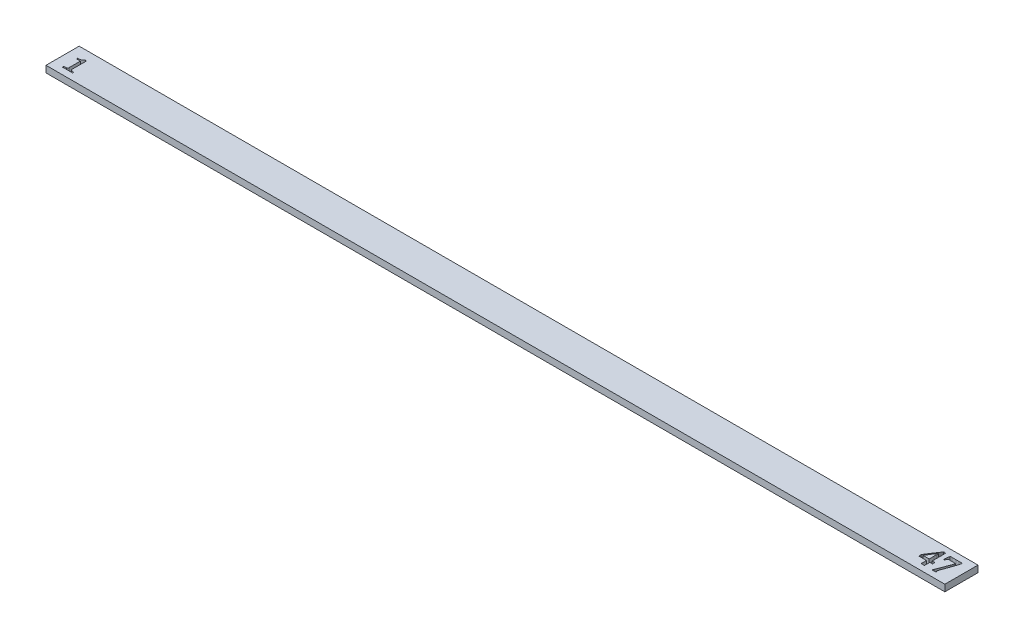
SolidWorks part; units mm, degrees
ref_plane "Front Plane" through (0, 0, 0) normal (0, 0, 1) x (1, 0, 0)
ref_plane "Top Plane" through (0, 0, 0) normal (0, 1, 0) x (1, 0, 0)
ref_plane "Right Plane" through (0, 0, 0) normal (1, 0, 0) x (0, 0, -1)
sketch "Sketch1" plane through (0, 0, 0) normal (0, 1, 0) x (1, 0, 0)
  line L1 (0, 0) -> (406.5, 0)
  line L2 (0, 0) -> (0, 15)
  line L3 (0, 15) -> (406.5, 15)
  line L4 (406.5, 0) -> (406.5, 15)
  dimension "D1" = 406.5
  dimension "D2" = 15
extrude "Boss-Extrude1" add sketch "Sketch1" along normal blind 3 contours L2 L1 L4 L3
sketch "Sketch6" plane through (0, 3, 0) normal (0, 1, 0) x (1, 0, 0)
  line L0 (9.0667, 3) -> (4.4, 3)
  line L1 (4.4, 3) -> (4.4, 3.5333)
  line L2 (6.1333, 4.4021) -> (6.1333, 9.4)
  line L3 (6.1333, 9.4) -> (4.4, 9.4)
  line L4 (4.4, 9.4) -> (4.4, 9.9333)
  line L5 (4.4, 9.9333) -> (4.7708, 9.9333)
  line L6 (6.9063, 10.8667) -> (7.4667, 10.8667)
  line L7 (7.4667, 8.6813) -> (7.4667, 4.4771)
  line L8 (9.0667, 3.5333) -> (9.0667, 3)
  spline S0 degree 3 poles (4.4, 3.5333) (4.4906, 3.5373) (4.6409, 3.5544) (4.8612, 3.5732) (5.0605, 3.5939) (5.2574, 3.6135) (5.4646, 3.6453) (5.603, 3.6659) (5.6813, 3.6896) knots 0 0 0 0 0.21039 0.351267 0.513318 0.675537 0.810763 1 1 1 1
  spline S1 degree 3 poles (5.6813, 3.6896) (5.7489, 3.7133) (5.8461, 3.7566) (5.9542, 3.8436) (6.0199, 3.9204) (6.0747, 4.0123) (6.1218, 4.1744) (6.1362, 4.3073) (6.1333, 4.4021) knots 0 0 0 0 0.235251 0.343488 0.451439 0.564461 0.690935 1 1 1 1
  spline S2 degree 3 poles (4.7708, 9.9333) (5.0033, 9.9326) (5.3457, 9.9689) (5.7802, 10.0922) (6.0742, 10.2224) (6.34, 10.3701) (6.6302, 10.5692) (6.8142, 10.7396) (6.9063, 10.8667) knots 0 0 0 0 0.289649 0.426683 0.561658 0.689593 0.805376 1 1 1 1
  spline S3 degree 3 poles (7.4667, 10.8667) (7.4667, 10.7) (7.4667, 10.4403) (7.4667, 10.0806) (7.4667, 9.5187) (7.4667, 9.05) (7.4667, 8.6813) knots 0 0 0 0 0.228789 0.35653 0.493804 1 1 1 1
  spline S4 degree 3 poles (7.4667, 4.4771) (7.4652, 4.3238) (7.5089, 4.1322) (7.6276, 3.9406) (7.7255, 3.8361) (7.8135, 3.7747) (7.8792, 3.7458) knots 0 0 0 0 0.518336 0.640812 0.758815 1 1 1 1
  spline S5 degree 3 poles (7.8792, 3.7458) (7.9543, 3.7133) (8.0861, 3.6778) (8.2812, 3.6344) (8.4608, 3.6037) (8.6413, 3.5752) (8.8434, 3.5503) (8.9822, 3.5352) (9.0667, 3.5333) knots 0 0 0 0 0.202205 0.337958 0.495327 0.653832 0.79092 1 1 1 1
extrude "Cut-Extrude3" cut sketch "Sketch6" against normal blind 3
sketch "Sketch7" plane through (0, 3, 0) normal (0, 1, 0) x (1, 0, 0)
  line L0 (0, 3) -> (406.5, 3)
  line L1 (0, 0) -> (0, 15) construction
  line L2 (406.5, 0) -> (406.5, 15) construction
  line L3 (0, 0) -> (406.5, 0) construction
  line L4 (397.6574, 12.1343) -> (399.3617, 12.1196)
  line L5 (399.3617, 12.1196) -> (400.8036, 12.1343)
  line L6 (400.8036, 12.1343) -> (401.6306, 12.1343)
  line L7 (401.6306, 12.1343) -> (401.916, 12.1343)
  line L8 (400.791, 7.2481) -> (400.4405, 6.2512)
  line L9 (400.1047, 5.3193) -> (399.5317, 3.7031)
  line L10 (399.5968, 2.7313) -> (399.4142, 2.7313)
  line L11 (399.4142, 2.7313) -> (398.8874, 2.7397)
  line L12 (399.007, 5.3046) -> (400.2642, 8.6943)
  line L13 (400.2642, 8.6943) -> (400.5791, 9.559)
  line L14 (399.7899, 10.5224) -> (398.7341, 10.5056)
  line L15 (398.7341, 10.5056) -> (397.8904, 10.5224)
  line L16 (395.7537, 6.2239) -> (395.7537, 5.1493)
  line L17 (394.5448, 4.9415) -> (394.5448, 4.5133)
  line L18 (394.5448, 4.5133) -> (394.5448, 4.0557)
  line L19 (394.5448, 4.0557) -> (394.5448, 3.7409)
  line L20 (394.5448, 2.7313) -> (393.9403, 2.7313)
  line L21 (393.9403, 2.7313) -> (393.5667, 2.7313)
  line L22 (393.3421, 2.7313) -> (393.2225, 2.7313)
  line L23 (393.0672, 2.7313) -> (393.0672, 4.1187)
  line L24 (393.0672, 4.1187) -> (393.0672, 5.0128)
  line L25 (392.0408, 5.1493) -> (391.5686, 5.1493)
  line L26 (389.5746, 5.1493) -> (389.5746, 5.2206)
  line L27 (389.5746, 5.2206) -> (389.5746, 5.6719)
  line L28 (389.5746, 5.6719) -> (389.5746, 5.8167)
  line L29 (389.5746, 5.8167) -> (389.5746, 6.0854)
  line L30 (389.5746, 6.0854) -> (389.5746, 6.1378)
  line L31 (389.9944, 6.9984) -> (391.6504, 9.559)
  line L32 (394.5448, 12.382) -> (394.5448, 12.2938)
  line L33 (394.5448, 12.2938) -> (394.5448, 11.746)
  line L34 (394.5448, 11.746) -> (394.5448, 11.555)
  line L35 (394.5448, 11.555) -> (394.5448, 11.2507)
  line L36 (394.5448, 11.2507) -> (394.5448, 10.9485)
  line L37 (394.5448, 10.9485) -> (394.5448, 10.216)
  line L38 (394.5448, 10.216) -> (394.5448, 9.899)
  line L39 (394.5448, 9.899) -> (394.5448, 9.4834)
  line L40 (394.5448, 9.4834) -> (394.5448, 9.0993)
  line L41 (394.5448, 9.0993) -> (394.5448, 8.5746)
  line L42 (394.5448, 8.5746) -> (394.5448, 8.073)
  line L43 (394.5448, 8.073) -> (394.5448, 7.4874)
  line L44 (394.5448, 7.4874) -> (394.5448, 6.2239)
  line L45 (395.2059, 6.2239) -> (395.3885, 6.2239)
  line L46 (393.0672, 7.4307) -> (393.0672, 7.9953)
  line L47 (393.0672, 7.9953) -> (393.0672, 8.4802)
  line L48 (393.0672, 8.4802) -> (393.0735, 9.7332)
  line L49 (393.0735, 9.7332) -> (393.0672, 10.3062)
  line L50 (392.0933, 9.2778) -> (391.4489, 8.2346)
  line L51 (390.6283, 6.3582) -> (390.9788, 6.3582)
  line L52 (390.9788, 6.3582) -> (391.6777, 6.3582)
  line L53 (391.6777, 6.3582) -> (392.6516, 6.3582)
  line L54 (392.6516, 6.3582) -> (393.0672, 6.3582)
  spline S0 degree 3 poles (396.7885, 12.1343) (396.9074, 12.1343) (397.1971, 12.1343) (397.4867, 12.1343) (397.6574, 12.1343) knots 0 0 0 0 0.410628 1 1 1 1
  spline S1 degree 2 poles (401.916, 12.1343) (402.0483, 12.1343) (402.1805, 12.1343) knots 0 0 0 1 1 1
  spline S2 degree 2 poles (402.1805, 12.1343) (402.2016, 11.9249) (402.2015, 11.7146) knots 0 0 0 1 1 1
  spline S3 degree 3 poles (402.2015, 11.7146) (402.2031, 11.6686) (402.1907, 11.5918) (402.1741, 11.4778) (402.1522, 11.3659) (402.1251, 11.2364) (402.0773, 11.0283) (402.0357, 10.8643) (402.0063, 10.7491) knots 0 0 0 0 0.13905 0.235946 0.350701 0.485483 0.638259 1 1 1 1
  spline S4 degree 3 poles (402.0063, 10.7491) (401.8713, 10.3858) (401.7226, 9.9355) (401.555, 9.4149) (401.4732, 9.1593) (401.4146, 8.9873) (401.3766, 8.8853) knots 0 0 0 0 0.590758 0.723007 0.834001 1 1 1 1
  spline S5 degree 3 poles (401.3766, 8.8853) (401.3139, 8.7235) (401.2049, 8.4219) (401.1038, 8.1175) (401.0618, 7.9764) knots 0 0 0 0 0.54115 1 1 1 1
  spline S6 degree 3 poles (401.0618, 7.9764) (401.0158, 7.8672) (400.9261, 7.6242) (400.8365, 7.3811) (400.791, 7.2481) knots 0 0 0 0 0.457479 1 1 1 1
  spline S7 degree 3 poles (400.4405, 6.2512) (400.4019, 6.129) (400.2893, 5.8185) (400.1773, 5.5079) (400.1047, 5.3193) knots 0 0 0 0 0.387978 1 1 1 1
  spline S8 degree 2 poles (399.5317, 3.7031) (399.4708, 3.5883) (399.4583, 3.4597) knots 0 0 0 1 1 1
  spline S9 degree 3 poles (399.4583, 3.4597) (399.4594, 3.4188) (399.4839, 3.3553) (399.5515, 3.2864) (399.6193, 3.235) (399.6889, 3.1853) (399.757, 3.1186) (399.7825, 3.0565) (399.7836, 3.0168) knots 0 0 0 0 0.21312 0.343422 0.503307 0.660927 0.793754 1 1 1 1
  spline S10 degree 3 poles (399.7836, 3.0168) (399.7823, 2.9669) (399.7381, 2.8546) (399.6492, 2.7737) (399.5968, 2.7313) knots 0 0 0 0 0.419347 1 1 1 1
  spline S11 degree 3 poles (398.8874, 2.7397) (398.8602, 2.7429) (398.809, 2.7411) (398.7271, 2.7429) (398.565, 2.7317) (398.4263, 2.7344) (398.3186, 2.7313) knots 0 0 0 0 0.143976 0.269387 0.431851 1 1 1 1
  spline S12 degree 2 poles (398.3186, 2.7313) (398.1779, 2.7313) (398.0373, 2.7313) knots 0 0 0 1 1 1
  spline S13 degree 3 poles (398.0373, 2.7313) (398.0497, 2.8378) (398.136, 3.1077) (398.2523, 3.3648) (398.3249, 3.5247) knots 0 0 0 0 0.377761 1 1 1 1
  spline S14 degree 3 poles (398.3249, 3.5247) (398.3592, 3.6042) (398.417, 3.7399) (398.4975, 3.9457) (398.5768, 4.1509) (398.6699, 4.3903) (398.8144, 4.7787) (398.9266, 5.0879) (399.007, 5.3046) knots 0 0 0 0 0.13619 0.232079 0.347806 0.482346 0.636339 1 1 1 1
  spline S15 degree 3 poles (400.5791, 9.559) (400.6161, 9.6353) (400.6856, 9.8169) (400.7493, 10.0004) (400.7826, 10.1047) knots 0 0 0 0 0.436195 1 1 1 1
  spline S16 degree 3 poles (400.7826, 10.1047) (400.7964, 10.1557) (400.8489, 10.2789) (400.8843, 10.4082) (400.917, 10.4825) knots 0 0 0 0 0.394055 1 1 1 1
  spline S17 degree 3 poles (400.917, 10.4825) (400.7072, 10.4941) (400.3316, 10.5116) (399.9558, 10.5235) (399.7899, 10.5224) knots 0 0 0 0 0.558859 1 1 1 1
  spline S18 degree 3 poles (397.8904, 10.5224) (397.7795, 10.5191) (397.6233, 10.5162) (397.4439, 10.4576) (397.3479, 10.402) (397.2801, 10.3185) (397.2259, 10.2157) (397.1823, 10.0881) (397.1537, 9.9447) (397.1276, 9.8052) (397.098, 9.6861) (397.0621, 9.5983) (397.0277, 9.5316) (396.9769, 9.4939) (396.8959, 9.4512) (396.8197, 9.4525) (396.7696, 9.4478) knots 0 0 0 0 0.189213 0.259177 0.317619 0.373826 0.438412 0.513621 0.600884 0.685342 0.753932 0.807539 0.846294 0.87826 0.912652 1 1 1 1
  spline S19 degree 3 poles (396.7696, 9.4478) (396.7096, 9.4441) (396.5726, 9.511) (396.5612, 9.6645) (396.5597, 9.7332) knots 0 0 0 0 0.447089 1 1 1 1
  spline S20 degree 3 poles (396.5597, 9.7332) (396.5577, 9.8826) (396.5859, 10.2424) (396.6123, 10.6021) (396.6395, 10.812) knots 0 0 0 0 0.413664 1 1 1 1
  spline S21 degree 3 poles (396.6395, 10.812) (396.6743, 11.0497) (396.712, 11.4917) (396.7566, 11.9331) (396.7885, 12.1343) knots 0 0 0 0 0.541005 1 1 1 1
  spline S22 degree 3 poles (395.7537, 5.1493) (395.6313, 5.1493) (395.4158, 5.1493) (395.2003, 5.1493) (395.1073, 5.1493) knots 0 0 0 0 0.568182 1 1 1 1
  spline S23 degree 2 poles (395.1073, 5.1493) (394.826, 5.1493) (394.5448, 5.1493) knots 0 0 0 1 1 1
  spline S24 degree 3 poles (394.5448, 5.1493) (394.5448, 5.1031) (394.5448, 5.0338) (394.5448, 4.9646) (394.5448, 4.9415) knots 0 0 0 0 0.666667 1 1 1 1
  spline S25 degree 3 poles (394.5448, 3.7409) (394.5448, 3.6905) (394.5448, 3.5471) (394.5448, 3.4037) (394.5448, 3.3106) knots 0 0 0 0 0.35122 1 1 1 1
  spline S26 degree 3 poles (394.5448, 3.3106) (394.5448, 3.2302) (394.5448, 3.0371) (394.5448, 2.844) (394.5448, 2.7313) knots 0 0 0 0 0.416667 1 1 1 1
  spline S27 degree 2 poles (393.5667, 2.7313) (393.4544, 2.7313) (393.3421, 2.7313) knots 0 0 0 1 1 1
  spline S28 degree 2 poles (393.2225, 2.7313) (393.1448, 2.7313) (393.0672, 2.7313) knots 0 0 0 1 1 1
  spline S29 degree 2 poles (393.0672, 5.0128) (393.0672, 5.081) (393.0672, 5.1493) knots 0 0 0 1 1 1
  spline S30 degree 3 poles (393.0672, 5.1493) (392.9244, 5.1493) (392.5823, 5.1493) (392.2402, 5.1493) (392.0408, 5.1493) knots 0 0 0 0 0.417178 1 1 1 1
  spline S31 degree 2 poles (391.5686, 5.1493) (390.8906, 5.1493) (390.2127, 5.1493) knots 0 0 0 1 1 1
  spline S32 degree 3 poles (390.2127, 5.1493) (390.1476, 5.1493) (390.0448, 5.1493) (389.9419, 5.1493) (389.9042, 5.1493) knots 0 0 0 0 0.632653 1 1 1 1
  spline S33 degree 2 poles (389.9042, 5.1493) (389.7394, 5.1493) (389.5746, 5.1493) knots 0 0 0 1 1 1
  spline S34 degree 3 poles (389.5746, 6.1378) (389.6238, 6.2444) (389.6936, 6.3963) (389.7862, 6.5855) (389.8422, 6.7026) (389.8904, 6.8013) (389.9392, 6.8983) (389.9714, 6.9628) (389.9944, 6.9984) knots 0 0 0 0 0.367667 0.523514 0.659761 0.774436 0.867544 1 1 1 1
  spline S35 degree 3 poles (391.6504, 9.559) (391.8071, 9.8063) (392.0391, 10.1441) (392.3248, 10.5655) (392.5022, 10.8076) (392.6506, 11.0139) (392.8031, 11.2258) (392.9004, 11.3743) (392.9559, 11.4648) knots 0 0 0 0 0.379956 0.532152 0.660989 0.769655 0.862163 1 1 1 1
  spline S36 degree 3 poles (392.9559, 11.4648) (393.0184, 11.5621) (393.122, 11.7417) (393.2461, 11.9077) (393.3001, 11.9811) knots 0 0 0 0 0.559034 1 1 1 1
  spline S37 degree 3 poles (393.3001, 11.9811) (393.3589, 12.0632) (393.4619, 12.1904) (393.5501, 12.3281) (393.5814, 12.382) knots 0 0 0 0 0.618512 1 1 1 1
  spline S38 degree 3 poles (393.5814, 12.382) (393.688, 12.3822) (393.8512, 12.402) (394.0152, 12.4001) (394.0725, 12.403) knots 0 0 0 0 0.649821 1 1 1 1
  spline S39 degree 3 poles (394.0725, 12.403) (394.1326, 12.4002) (394.2904, 12.4025) (394.4473, 12.383) (394.5448, 12.382) knots 0 0 0 0 0.381894 1 1 1 1
  spline S40 degree 2 poles (394.5448, 6.2239) (394.8753, 6.2239) (395.2059, 6.2239) knots 0 0 0 1 1 1
  spline S41 degree 2 poles (395.3885, 6.2239) (395.5711, 6.2239) (395.7537, 6.2239) knots 0 0 0 1 1 1
  spline S42 degree 3 poles (393.0672, 6.3582) (393.0672, 6.4639) (393.0672, 6.6451) (393.0672, 6.8263) (393.0672, 6.9018) knots 0 0 0 0 0.583012 1 1 1 1
  spline S43 degree 3 poles (393.0672, 6.9018) (393.0672, 6.9921) (393.0672, 7.1124) (393.0672, 7.2572) (393.0672, 7.3433) (393.0672, 7.3993) (393.0672, 7.4307) knots 0 0 0 0 0.511905 0.68254 0.821429 1 1 1 1
  spline S44 degree 3 poles (393.0672, 10.3062) (393.0654, 10.3469) (393.0754, 10.46) (393.076, 10.5736) (393.0819, 10.6462) knots 0 0 0 0 0.357984 1 1 1 1
  spline S45 degree 2 poles (393.0819, 10.6462) (392.9879, 10.5109) (392.8804, 10.386) knots 0 0 0 1 1 1
  spline S46 degree 2 poles (392.8804, 10.386) (392.8063, 10.2569) (392.7167, 10.1383) knots 0 0 0 1 1 1
  spline S47 degree 3 poles (392.7167, 10.1383) (392.6149, 10.0112) (392.4005, 9.729) (392.1991, 9.4374) (392.0933, 9.2778) knots 0 0 0 0 0.459339 1 1 1 1
  spline S48 degree 2 poles (391.4489, 8.2346) (391.3415, 8.0668) (391.2411, 7.8946) knots 0 0 0 1 1 1
  spline S49 degree 3 poles (391.2411, 7.8946) (391.0913, 7.6473) (390.7622, 7.1508) (390.4554, 6.6391) (390.3302, 6.3582) knots 0 0 0 0 0.485064 1 1 1 1
  spline S50 degree 3 poles (390.3302, 6.3582) (390.3918, 6.3582) (390.4911, 6.3582) (390.5905, 6.3582) (390.6283, 6.3582) knots 0 0 0 0 0.619718 1 1 1 1
  dimension "D1" = 3
extrude "Cut-Extrude4" cut sketch "Sketch7" against normal through all both and the other way through all contours S21 S20 S19 S18 L15 L14 S17 S16 S15 L13 L12 S14 S13 L0 S10 S9 S8 L9 S7 L8 S6 S5 S4 S3 S2 S1 L7 L6 L5 L4 S0 | S41 L45 S40 L44 L43 L42 L41 L40 L39 L38 L37 L36 L35 L34 L33 L32 S39 S38 S37 S36 S35 L31 S34 L30 L29 L28 L27 L26 S33 S32 S31 L25 S30 S29 L24 L23 L0 S26 S25 L19 L18 L17 S24 S23 S22 L16 S50 S49 S48 L50 | S28 L22 S27 L21 L20 S26 L0 L23
